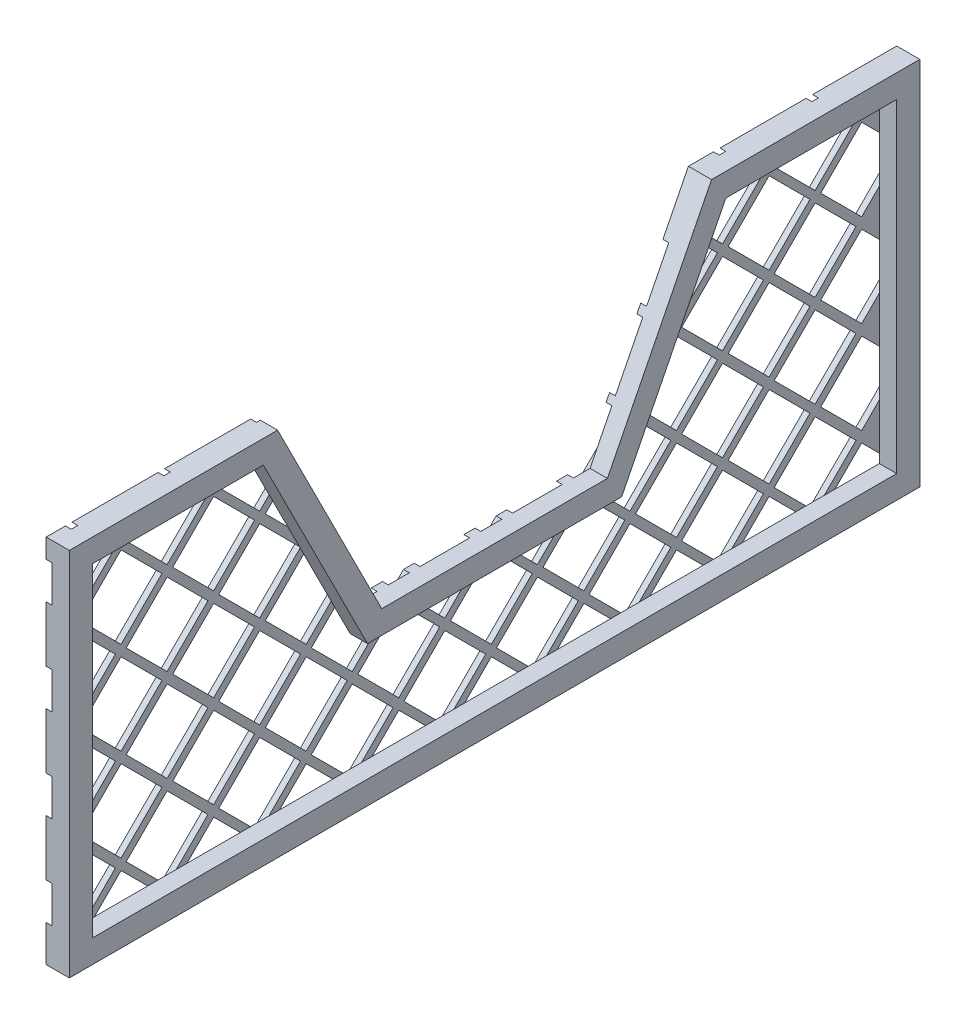
SolidWorks part; units mm, degrees
ref_plane "Front" through (0, 0, 0) normal (0, 0, 1) x (1, 0, 0)
ref_plane "Top" through (0, 0, 0) normal (0, 1, 0) x (1, 0, 0)
ref_plane "Right" through (0, 0, 0) normal (1, 0, 0) x (0, 0, -1)
sketch "Sketch1" plane through (0, 0, 0) normal (1, 0, 0) x (0, 0, -1)
  line L0 (-163.8892, 74.3605) -> (-49.5892, 74.3605)
  line L1 (-49.5892, 74.3605) -> (7.5608, -39.0542)
  line L2 (7.5608, -39.0542) -> (131.3858, -39.0542)
  line L3 (131.3858, -39.0542) -> (188.5358, 74.3605)
  line L4 (188.5358, 74.3605) -> (302.8358, 74.3605)
  line L5 (302.8358, 74.3605) -> (302.8358, -128.8395)
  line L6 (302.8358, -128.8395) -> (-163.8892, -128.8395)
  line L7 (-163.8892, -128.8395) -> (-163.8892, 74.3605)
  line L16 (290.1358, 61.6605) -> (290.1358, -116.1395)
  line L17 (290.1358, -116.1395) -> (-151.1892, -116.1395)
  line L18 (-151.1892, -116.1395) -> (-151.1892, 61.6605)
  line L19 (-151.1892, 61.6605) -> (-57.4109, 61.6605)
  line L20 (-57.4109, 61.6605) -> (-0.2609, -51.7542)
  line L21 (-0.2609, -51.7542) -> (139.2075, -51.7542)
  line L22 (139.2075, -51.7542) -> (196.3575, 61.6605)
  line L23 (196.3575, 61.6605) -> (290.1358, 61.6605)
  dimension "D1" = 466.725
  dimension "D2" = 203.2
  dimension "D3" = 123.825
  dimension "D4" = 114.3
  dimension "D5" = 114.3
  dimension "D6" = 127
  dimension "D7" = 127
  dimension "D8" = 203.2
  dimension "D9" = 12.7
extrude "Boss-Extrude1" add sketch "Sketch1" along normal blind 12.7
sketch "Sketch4" plane through (0, 0, 0) normal (-1, 0, 0) x (0, 0, 1)
  line L0 (-290.1358, 61.6605) -> (-196.3575, 61.6605)
  line L1 (-196.3575, 61.6605) -> (-139.2075, -51.7542)
  line L2 (-139.2075, -51.7542) -> (0.2609, -51.7542)
  line L3 (0.2609, -51.7542) -> (57.4109, 61.6605)
  line L4 (57.4109, 61.6605) -> (151.1892, 61.6605)
  line L5 (151.1892, 61.6605) -> (151.1892, -116.1395)
  line L6 (151.1892, -116.1395) -> (-290.1358, -116.1395)
  line L7 (-290.1358, -116.1395) -> (-290.1358, 61.6605)
extrude "Boss-Extrude4" add sketch "Sketch4" against normal blind 3.175
sketch "Sketch6" plane through (3.175, 0, 0) normal (1, 0, 0) x (0, 0, -1)
  line L0 (-148.4172, 28.4356) -> (-125.9666, 50.8862)
  line L1 (-125.9666, 50.8862) -> (-103.5159, 28.4356)
  line L2 (-148.4172, 28.4356) -> (-125.9666, 5.9849)
  line L3 (-125.9666, 5.9849) -> (-103.5159, 28.4356)
  line L4 (-151.5103, 76.1424) -> (-129.0597, 53.6918)
  line L5 (-129.0597, 53.6918) -> (-151.5103, 31.2412)
  line L6 (-151.5103, 31.2412) -> (-173.961, 53.6918)
  line L7 (-173.961, 53.6918) -> (-151.5103, 76.1424)
  line L8 (-97.6172, 28.4356) -> (-75.1666, 50.8862)
  line L9 (-75.1666, 50.8862) -> (-52.7159, 28.4356)
  line L10 (-97.6172, 28.4356) -> (-75.1666, 5.9849)
  line L11 (-75.1666, 5.9849) -> (-52.7159, 28.4356)
  line L12 (-100.7103, 31.2412) -> (-123.161, 53.6918)
  line L13 (-123.161, 53.6918) -> (-100.7103, 76.1424)
  line L14 (-100.7103, 76.1424) -> (-78.2597, 53.6918)
  line L15 (-78.2597, 53.6918) -> (-100.7103, 31.2412)
  line L16 (-46.8172, 28.4356) -> (-24.3666, 50.8862)
  line L17 (-24.3666, 50.8862) -> (-1.9159, 28.4356)
  line L18 (-46.8172, 28.4356) -> (-24.3666, 5.9849)
  line L19 (-24.3666, 5.9849) -> (-1.9159, 28.4356)
  line L20 (-49.9103, 31.2412) -> (-72.361, 53.6918)
  line L21 (-72.361, 53.6918) -> (-49.9103, 76.1424)
  line L22 (-49.9103, 76.1424) -> (-27.4597, 53.6918)
  line L23 (-27.4597, 53.6918) -> (-49.9103, 31.2412)
  line L24 (3.9828, 28.4356) -> (26.4334, 50.8862)
  line L25 (26.4334, 50.8862) -> (48.8841, 28.4356)
  line L26 (3.9828, 28.4356) -> (26.4334, 5.9849)
  line L27 (26.4334, 5.9849) -> (48.8841, 28.4356)
  line L28 (0.8897, 31.2412) -> (-21.561, 53.6918)
  line L29 (-21.561, 53.6918) -> (0.8897, 76.1424)
  line L30 (0.8897, 76.1424) -> (23.3403, 53.6918)
  line L31 (23.3403, 53.6918) -> (0.8897, 31.2412)
  line L32 (54.7828, 28.4356) -> (77.2334, 50.8862)
  line L33 (77.2334, 50.8862) -> (99.6841, 28.4356)
  line L34 (54.7828, 28.4356) -> (77.2334, 5.9849)
  line L35 (77.2334, 5.9849) -> (99.6841, 28.4356)
  line L36 (51.6897, 31.2412) -> (29.239, 53.6918)
  line L37 (29.239, 53.6918) -> (51.6897, 76.1424)
  line L38 (51.6897, 76.1424) -> (74.1403, 53.6918)
  line L39 (74.1403, 53.6918) -> (51.6897, 31.2412)
  line L40 (105.5828, 28.4356) -> (128.0334, 50.8862)
  line L41 (128.0334, 50.8862) -> (150.4841, 28.4356)
  line L42 (105.5828, 28.4356) -> (128.0334, 5.9849)
  line L43 (128.0334, 5.9849) -> (150.4841, 28.4356)
  line L44 (102.4897, 31.2412) -> (80.039, 53.6918)
  line L45 (80.039, 53.6918) -> (102.4897, 76.1424)
  line L46 (102.4897, 76.1424) -> (124.9403, 53.6918)
  line L47 (124.9403, 53.6918) -> (102.4897, 31.2412)
  line L48 (156.3828, 28.4356) -> (178.8334, 50.8862)
  line L49 (178.8334, 50.8862) -> (201.2841, 28.4356)
  line L50 (156.3828, 28.4356) -> (178.8334, 5.9849)
  line L51 (178.8334, 5.9849) -> (201.2841, 28.4356)
  line L52 (153.2897, 31.2412) -> (130.839, 53.6918)
  line L53 (130.839, 53.6918) -> (153.2897, 76.1424)
  line L54 (153.2897, 76.1424) -> (175.7403, 53.6918)
  line L55 (175.7403, 53.6918) -> (153.2897, 31.2412)
  line L56 (207.1828, 28.4356) -> (229.6334, 50.8862)
  line L57 (229.6334, 50.8862) -> (252.0841, 28.4356)
  line L58 (207.1828, 28.4356) -> (229.6334, 5.9849)
  line L59 (229.6334, 5.9849) -> (252.0841, 28.4356)
  line L60 (204.0897, 31.2412) -> (181.639, 53.6918)
  line L61 (181.639, 53.6918) -> (204.0897, 76.1424)
  line L62 (204.0897, 76.1424) -> (226.5403, 53.6918)
  line L63 (226.5403, 53.6918) -> (204.0897, 31.2412)
  line L64 (257.9828, 28.4356) -> (280.4334, 50.8862)
  line L65 (280.4334, 50.8862) -> (302.8841, 28.4356)
  line L66 (257.9828, 28.4356) -> (280.4334, 5.9849)
  line L67 (280.4334, 5.9849) -> (302.8841, 28.4356)
  line L68 (254.8897, 31.2412) -> (232.439, 53.6918)
  line L69 (232.439, 53.6918) -> (254.8897, 76.1424)
  line L70 (254.8897, 76.1424) -> (277.3403, 53.6918)
  line L71 (277.3403, 53.6918) -> (254.8897, 31.2412)
  line L72 (-97.6172, -22.3644) -> (-75.1666, 0.0862)
  line L73 (-75.1666, 0.0862) -> (-52.7159, -22.3644)
  line L74 (-97.6172, -22.3644) -> (-75.1666, -44.8151)
  line L75 (-75.1666, -44.8151) -> (-52.7159, -22.3644)
  line L76 (-100.7103, -19.5588) -> (-123.161, 2.8918)
  line L77 (-123.161, 2.8918) -> (-100.7103, 25.3424)
  line L78 (-100.7103, 25.3424) -> (-78.2597, 2.8918)
  line L79 (-78.2597, 2.8918) -> (-100.7103, -19.5588)
  line L80 (-46.8172, -22.3644) -> (-24.3666, 0.0862)
  line L81 (-24.3666, 0.0862) -> (-1.9159, -22.3644)
  line L82 (-46.8172, -22.3644) -> (-24.3666, -44.8151)
  line L83 (-24.3666, -44.8151) -> (-1.9159, -22.3644)
  line L84 (-49.9103, -19.5588) -> (-72.361, 2.8918)
  line L85 (-72.361, 2.8918) -> (-49.9103, 25.3424)
  line L86 (-49.9103, 25.3424) -> (-27.4597, 2.8918)
  line L87 (-27.4597, 2.8918) -> (-49.9103, -19.5588)
  line L88 (3.9828, -22.3644) -> (26.4334, 0.0862)
  line L89 (26.4334, 0.0862) -> (48.8841, -22.3644)
  line L90 (3.9828, -22.3644) -> (26.4334, -44.8151)
  line L91 (26.4334, -44.8151) -> (48.8841, -22.3644)
  line L92 (0.8897, -19.5588) -> (-21.561, 2.8918)
  line L93 (-21.561, 2.8918) -> (0.8897, 25.3424)
  line L94 (0.8897, 25.3424) -> (23.3403, 2.8918)
  line L95 (23.3403, 2.8918) -> (0.8897, -19.5588)
  line L96 (54.7828, -22.3644) -> (77.2334, 0.0862)
  line L97 (77.2334, 0.0862) -> (99.6841, -22.3644)
  line L98 (54.7828, -22.3644) -> (77.2334, -44.8151)
  line L99 (77.2334, -44.8151) -> (99.6841, -22.3644)
  line L100 (51.6897, -19.5588) -> (29.239, 2.8918)
  line L101 (29.239, 2.8918) -> (51.6897, 25.3424)
  line L102 (51.6897, 25.3424) -> (74.1403, 2.8918)
  line L103 (74.1403, 2.8918) -> (51.6897, -19.5588)
  line L104 (105.5828, -22.3644) -> (128.0334, 0.0862)
  line L105 (128.0334, 0.0862) -> (150.4841, -22.3644)
  line L106 (105.5828, -22.3644) -> (128.0334, -44.8151)
  line L107 (128.0334, -44.8151) -> (150.4841, -22.3644)
  line L108 (102.4897, -19.5588) -> (80.039, 2.8918)
  line L109 (80.039, 2.8918) -> (102.4897, 25.3424)
  line L110 (102.4897, 25.3424) -> (124.9403, 2.8918)
  line L111 (124.9403, 2.8918) -> (102.4897, -19.5588)
  line L112 (156.3828, -22.3644) -> (178.8334, 0.0862)
  line L113 (178.8334, 0.0862) -> (201.2841, -22.3644)
  line L114 (156.3828, -22.3644) -> (178.8334, -44.8151)
  line L115 (178.8334, -44.8151) -> (201.2841, -22.3644)
  line L116 (153.2897, -19.5588) -> (130.839, 2.8918)
  line L117 (130.839, 2.8918) -> (153.2897, 25.3424)
  line L118 (153.2897, 25.3424) -> (175.7403, 2.8918)
  line L119 (175.7403, 2.8918) -> (153.2897, -19.5588)
  line L120 (207.1828, -22.3644) -> (229.6334, 0.0862)
  line L121 (229.6334, 0.0862) -> (252.0841, -22.3644)
  line L122 (207.1828, -22.3644) -> (229.6334, -44.8151)
  line L123 (229.6334, -44.8151) -> (252.0841, -22.3644)
  line L124 (204.0897, -19.5588) -> (181.639, 2.8918)
  line L125 (181.639, 2.8918) -> (204.0897, 25.3424)
  line L126 (204.0897, 25.3424) -> (226.5403, 2.8918)
  line L127 (226.5403, 2.8918) -> (204.0897, -19.5588)
  line L128 (257.9828, -22.3644) -> (280.4334, 0.0862)
  line L129 (280.4334, 0.0862) -> (302.8841, -22.3644)
  line L130 (257.9828, -22.3644) -> (280.4334, -44.8151)
  line L131 (280.4334, -44.8151) -> (302.8841, -22.3644)
  line L132 (254.8897, -19.5588) -> (232.439, 2.8918)
  line L133 (232.439, 2.8918) -> (254.8897, 25.3424)
  line L134 (254.8897, 25.3424) -> (277.3403, 2.8918)
  line L135 (277.3403, 2.8918) -> (254.8897, -19.5588)
  line L136 (-97.6172, -73.1644) -> (-75.1666, -50.7138)
  line L137 (-75.1666, -50.7138) -> (-52.7159, -73.1644)
  line L138 (-97.6172, -73.1644) -> (-75.1666, -95.6151)
  line L139 (-75.1666, -95.6151) -> (-52.7159, -73.1644)
  line L140 (-100.7103, -70.3588) -> (-123.161, -47.9082)
  line L141 (-123.161, -47.9082) -> (-100.7103, -25.4576)
  line L142 (-100.7103, -25.4576) -> (-78.2597, -47.9082)
  line L143 (-78.2597, -47.9082) -> (-100.7103, -70.3588)
  line L144 (-46.8172, -73.1644) -> (-24.3666, -50.7138)
  line L145 (-24.3666, -50.7138) -> (-1.9159, -73.1644)
  line L146 (-46.8172, -73.1644) -> (-24.3666, -95.6151)
  line L147 (-24.3666, -95.6151) -> (-1.9159, -73.1644)
  line L148 (-49.9103, -70.3588) -> (-72.361, -47.9082)
  line L149 (-72.361, -47.9082) -> (-49.9103, -25.4576)
  line L150 (-49.9103, -25.4576) -> (-27.4597, -47.9082)
  line L151 (-27.4597, -47.9082) -> (-49.9103, -70.3588)
  line L152 (3.9828, -73.1644) -> (26.4334, -50.7138)
  line L153 (26.4334, -50.7138) -> (48.8841, -73.1644)
  line L154 (3.9828, -73.1644) -> (26.4334, -95.6151)
  line L155 (26.4334, -95.6151) -> (48.8841, -73.1644)
  line L156 (0.8897, -70.3588) -> (-21.561, -47.9082)
  line L157 (-21.561, -47.9082) -> (0.8897, -25.4576)
  line L158 (0.8897, -25.4576) -> (23.3403, -47.9082)
  line L159 (23.3403, -47.9082) -> (0.8897, -70.3588)
  line L160 (54.7828, -73.1644) -> (77.2334, -50.7138)
  line L161 (77.2334, -50.7138) -> (99.6841, -73.1644)
  line L162 (54.7828, -73.1644) -> (77.2334, -95.6151)
  line L163 (77.2334, -95.6151) -> (99.6841, -73.1644)
  line L164 (51.6897, -70.3588) -> (29.239, -47.9082)
  line L165 (29.239, -47.9082) -> (51.6897, -25.4576)
  line L166 (51.6897, -25.4576) -> (74.1403, -47.9082)
  line L167 (74.1403, -47.9082) -> (51.6897, -70.3588)
  line L168 (105.5828, -73.1644) -> (128.0334, -50.7138)
  line L169 (128.0334, -50.7138) -> (150.4841, -73.1644)
  line L170 (105.5828, -73.1644) -> (128.0334, -95.6151)
  line L171 (128.0334, -95.6151) -> (150.4841, -73.1644)
  line L172 (102.4897, -70.3588) -> (80.039, -47.9082)
  line L173 (80.039, -47.9082) -> (102.4897, -25.4576)
  line L174 (102.4897, -25.4576) -> (124.9403, -47.9082)
  line L175 (124.9403, -47.9082) -> (102.4897, -70.3588)
  line L176 (156.3828, -73.1644) -> (178.8334, -50.7138)
  line L177 (178.8334, -50.7138) -> (201.2841, -73.1644)
  line L178 (156.3828, -73.1644) -> (178.8334, -95.6151)
  line L179 (178.8334, -95.6151) -> (201.2841, -73.1644)
  line L180 (153.2897, -70.3588) -> (130.839, -47.9082)
  line L181 (130.839, -47.9082) -> (153.2897, -25.4576)
  line L182 (153.2897, -25.4576) -> (175.7403, -47.9082)
  line L183 (175.7403, -47.9082) -> (153.2897, -70.3588)
  line L184 (207.1828, -73.1644) -> (229.6334, -50.7138)
  line L185 (229.6334, -50.7138) -> (252.0841, -73.1644)
  line L186 (207.1828, -73.1644) -> (229.6334, -95.6151)
  line L187 (229.6334, -95.6151) -> (252.0841, -73.1644)
  line L188 (204.0897, -70.3588) -> (181.639, -47.9082)
  line L189 (181.639, -47.9082) -> (204.0897, -25.4576)
  line L190 (204.0897, -25.4576) -> (226.5403, -47.9082)
  line L191 (226.5403, -47.9082) -> (204.0897, -70.3588)
  line L192 (257.9828, -73.1644) -> (280.4334, -50.7138)
  line L193 (280.4334, -50.7138) -> (302.8841, -73.1644)
  line L194 (257.9828, -73.1644) -> (280.4334, -95.6151)
  line L195 (280.4334, -95.6151) -> (302.8841, -73.1644)
  line L196 (254.8897, -70.3588) -> (232.439, -47.9082)
  line L197 (232.439, -47.9082) -> (254.8897, -25.4576)
  line L198 (254.8897, -25.4576) -> (277.3403, -47.9082)
  line L199 (277.3403, -47.9082) -> (254.8897, -70.3588)
  line L200 (-97.6172, -123.9644) -> (-75.1666, -101.5138)
  line L201 (-75.1666, -101.5138) -> (-52.7159, -123.9644)
  line L202 (-97.6172, -123.9644) -> (-75.1666, -146.4151)
  line L203 (-75.1666, -146.4151) -> (-52.7159, -123.9644)
  line L204 (-100.7103, -121.1588) -> (-123.161, -98.7082)
  line L205 (-123.161, -98.7082) -> (-100.7103, -76.2576)
  line L206 (-100.7103, -76.2576) -> (-78.2597, -98.7082)
  line L207 (-78.2597, -98.7082) -> (-100.7103, -121.1588)
  line L208 (-46.8172, -123.9644) -> (-24.3666, -101.5138)
  line L209 (-24.3666, -101.5138) -> (-1.9159, -123.9644)
  line L210 (-46.8172, -123.9644) -> (-24.3666, -146.4151)
  line L211 (-24.3666, -146.4151) -> (-1.9159, -123.9644)
  line L212 (-49.9103, -121.1588) -> (-72.361, -98.7082)
  line L213 (-72.361, -98.7082) -> (-49.9103, -76.2576)
  line L214 (-49.9103, -76.2576) -> (-27.4597, -98.7082)
  line L215 (-27.4597, -98.7082) -> (-49.9103, -121.1588)
  line L216 (3.9828, -123.9644) -> (26.4334, -101.5138)
  line L217 (26.4334, -101.5138) -> (48.8841, -123.9644)
  line L218 (3.9828, -123.9644) -> (26.4334, -146.4151)
  line L219 (26.4334, -146.4151) -> (48.8841, -123.9644)
  line L220 (0.8897, -121.1588) -> (-21.561, -98.7082)
  line L221 (-21.561, -98.7082) -> (0.8897, -76.2576)
  line L222 (0.8897, -76.2576) -> (23.3403, -98.7082)
  line L223 (23.3403, -98.7082) -> (0.8897, -121.1588)
  line L224 (54.7828, -123.9644) -> (77.2334, -101.5138)
  line L225 (77.2334, -101.5138) -> (99.6841, -123.9644)
  line L226 (54.7828, -123.9644) -> (77.2334, -146.4151)
  line L227 (77.2334, -146.4151) -> (99.6841, -123.9644)
  line L228 (51.6897, -121.1588) -> (29.239, -98.7082)
  line L229 (29.239, -98.7082) -> (51.6897, -76.2576)
  line L230 (51.6897, -76.2576) -> (74.1403, -98.7082)
  line L231 (74.1403, -98.7082) -> (51.6897, -121.1588)
  line L232 (105.5828, -123.9644) -> (128.0334, -101.5138)
  line L233 (128.0334, -101.5138) -> (150.4841, -123.9644)
  line L234 (105.5828, -123.9644) -> (128.0334, -146.4151)
  line L235 (128.0334, -146.4151) -> (150.4841, -123.9644)
  line L236 (102.4897, -121.1588) -> (80.039, -98.7082)
  line L237 (80.039, -98.7082) -> (102.4897, -76.2576)
  line L238 (102.4897, -76.2576) -> (124.9403, -98.7082)
  line L239 (124.9403, -98.7082) -> (102.4897, -121.1588)
  line L240 (156.3828, -123.9644) -> (178.8334, -101.5138)
  line L241 (178.8334, -101.5138) -> (201.2841, -123.9644)
  line L242 (156.3828, -123.9644) -> (178.8334, -146.4151)
  line L243 (178.8334, -146.4151) -> (201.2841, -123.9644)
  line L244 (153.2897, -121.1588) -> (130.839, -98.7082)
  line L245 (130.839, -98.7082) -> (153.2897, -76.2576)
  line L246 (153.2897, -76.2576) -> (175.7403, -98.7082)
  line L247 (175.7403, -98.7082) -> (153.2897, -121.1588)
  line L248 (207.1828, -123.9644) -> (229.6334, -101.5138)
  line L249 (229.6334, -101.5138) -> (252.0841, -123.9644)
  line L250 (207.1828, -123.9644) -> (229.6334, -146.4151)
  line L251 (229.6334, -146.4151) -> (252.0841, -123.9644)
  line L252 (204.0897, -121.1588) -> (181.639, -98.7082)
  line L253 (181.639, -98.7082) -> (204.0897, -76.2576)
  line L254 (204.0897, -76.2576) -> (226.5403, -98.7082)
  line L255 (226.5403, -98.7082) -> (204.0897, -121.1588)
  line L256 (257.9828, -123.9644) -> (280.4334, -101.5138)
  line L257 (280.4334, -101.5138) -> (302.8841, -123.9644)
  line L258 (257.9828, -123.9644) -> (280.4334, -146.4151)
  line L259 (280.4334, -146.4151) -> (302.8841, -123.9644)
  line L260 (254.8897, -121.1588) -> (232.439, -98.7082)
  line L261 (232.439, -98.7082) -> (254.8897, -76.2576)
  line L262 (254.8897, -76.2576) -> (277.3403, -98.7082)
  line L263 (277.3403, -98.7082) -> (254.8897, -121.1588)
  line L264 (-148.4172, -22.3644) -> (-125.9666, 0.0862)
  line L265 (-125.9666, 0.0862) -> (-103.5159, -22.3644)
  line L266 (-148.4172, -22.3644) -> (-125.9666, -44.8151)
  line L267 (-125.9666, -44.8151) -> (-103.5159, -22.3644)
  line L268 (-151.5103, -19.5588) -> (-173.961, 2.8918)
  line L269 (-173.961, 2.8918) -> (-151.5103, 25.3424)
  line L270 (-151.5103, 25.3424) -> (-129.0597, 2.8918)
  line L271 (-129.0597, 2.8918) -> (-151.5103, -19.5588)
  line L272 (-148.4172, -73.1644) -> (-125.9666, -50.7138)
  line L273 (-125.9666, -50.7138) -> (-103.5159, -73.1644)
  line L274 (-148.4172, -73.1644) -> (-125.9666, -95.6151)
  line L275 (-125.9666, -95.6151) -> (-103.5159, -73.1644)
  line L276 (-151.5103, -70.3588) -> (-173.961, -47.9082)
  line L277 (-173.961, -47.9082) -> (-151.5103, -25.4576)
  line L278 (-151.5103, -25.4576) -> (-129.0597, -47.9082)
  line L279 (-129.0597, -47.9082) -> (-151.5103, -70.3588)
  line L280 (-148.4172, -123.9644) -> (-125.9666, -101.5138)
  line L281 (-125.9666, -101.5138) -> (-103.5159, -123.9644)
  line L282 (-148.4172, -123.9644) -> (-125.9666, -146.4151)
  line L283 (-125.9666, -146.4151) -> (-103.5159, -123.9644)
  line L284 (-151.5103, -121.1588) -> (-173.961, -98.7082)
  line L285 (-173.961, -98.7082) -> (-151.5103, -76.2576)
  line L286 (-151.5103, -76.2576) -> (-129.0597, -98.7082)
  line L287 (-129.0597, -98.7082) -> (-151.5103, -121.1588)
  dimension "D1" = 9
  dimension "D2" = 4
extrude "Cut-Extrude2" cut sketch "Sketch6" against normal blind 3.175
